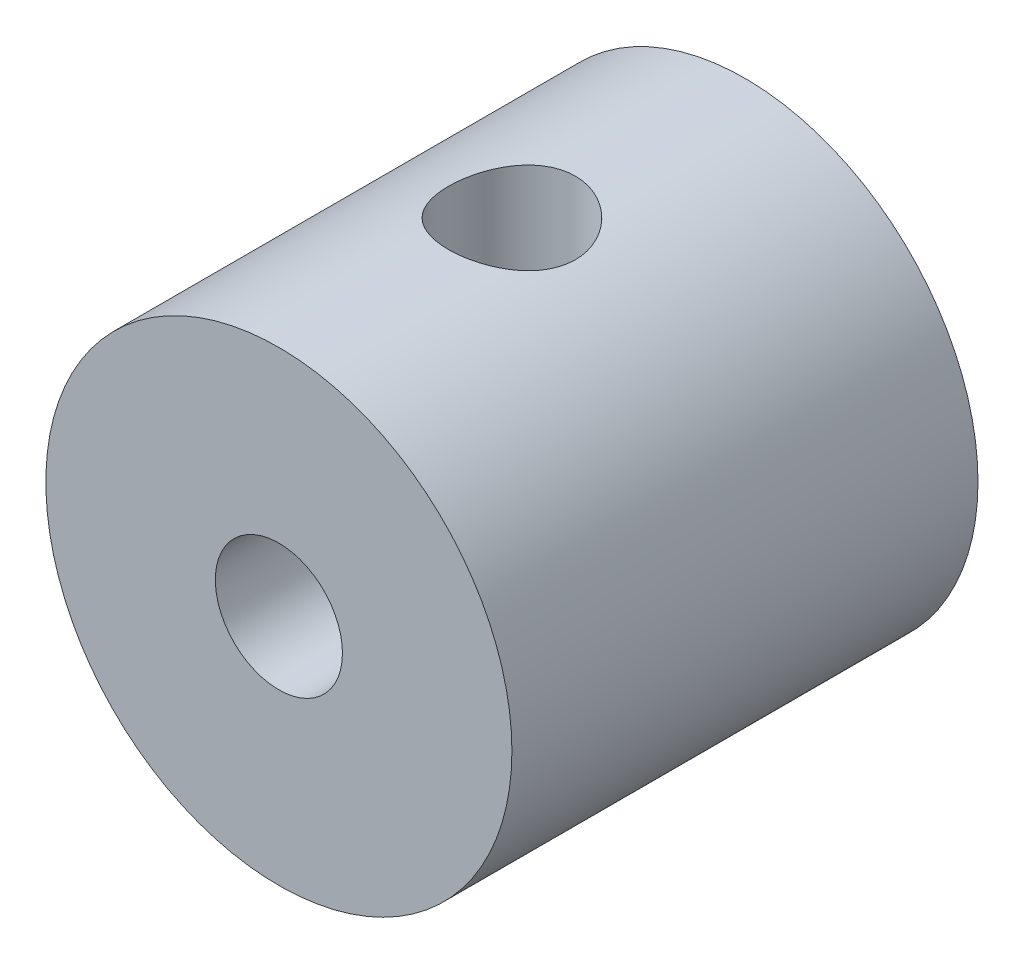
SolidWorks part; units mm, degrees
ref_plane "前视基准面" through (0, 0, 0) normal (0, 0, 1) x (1, 0, 0)
ref_plane "上视基准面" through (0, 0, 0) normal (0, 1, 0) x (1, 0, 0)
ref_plane "右视基准面" through (0, 0, 0) normal (1, 0, 0) x (0, 0, -1)
sketch "草图1" plane through (0, 0, 0) normal (0, 0, 1) x (1, 0, 0)
  circle A0 centre (0, 0) radius 2.75
  circle A1 centre (0, 0) radius 0.75
  dimension "D1" = 5.5
  dimension "D2" = 1.5
extrude "凸台-拉伸1" add sketch "草图1" along normal blind 5.5
sketch "草图2" plane through (0, 0, 0) normal (0, 1, 0) x (1, 0, 0)
  line L0 (0, 1.1505) -> (0, -6.8154) construction
  line L1 (-5.6319, -2.75) -> (5.6446, -2.75) construction
  line L2 (2.75, 0) -> (-2.75, 0) construction
  line L3 (-2.75, -5.5) -> (2.75, -5.5) construction
  circle A0 centre (0, -2.75) radius 0.75
  dimension "D1" = 1.5
extrude "切除-拉伸1" cut sketch "草图2" against normal mid plane 5.5
